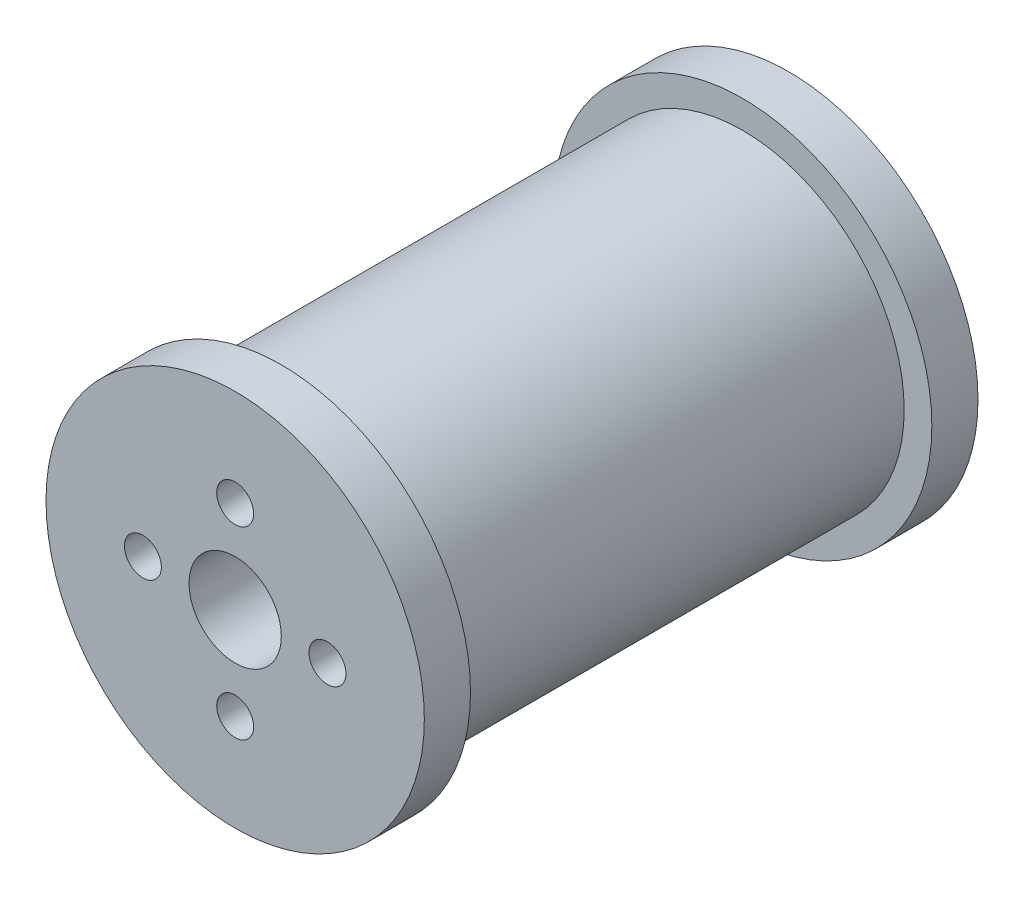
SolidWorks part; units mm, degrees
material "PET"
ref_plane "Front Plane" through (0, 0, 0) normal (0, 0, 1) x (1, 0, 0)
ref_plane "Top Plane" through (0, 0, 0) normal (0, 1, 0) x (1, 0, 0)
ref_plane "Right Plane" through (0, 0, 0) normal (1, 0, 0) x (0, 0, -1)
sketch "Sketch1" plane through (0, 0, 0) normal (0, 0, 1) x (1, 0, 0)
  circle A0 centre (0, 0) radius 17.5
  circle A1 centre (0, 0) radius 5
  circle A2 centre (0, 0) radius 10 construction
  circle A3 centre (0, 10) radius 2
  circle A4 centre (10, 0) radius 2
  circle A5 centre (0, -10) radius 2
  circle A6 centre (-10, 0) radius 2
  point P16 (0, 0)
  dimension "D1" = 35
  dimension "D2" = 10
  dimension "D3" = 20
  dimension "D4" = 4
  dimension "D5" = 4
extrude "Boss-Extrude1" add sketch "Sketch1" along normal blind 50
sketch "Sketch2" plane through (0, 0, 50) normal (0, 0, 1) x (1, 0, 0)
  circle A0 centre (0, 0) radius 20.5
  circle A1 centre (0, 0) radius 17.5 construction
  circle A2 centre (0, 0) radius 5
  circle A3 centre (0, 0) radius 5 construction
  circle A4 centre (0, 0) radius 10 construction
  circle A5 centre (0, 10) radius 2
  circle A6 centre (0, 0) radius 20.5
  circle A7 centre (10, 0) radius 2
  circle A8 centre (0, 0) radius 20.5
  circle A9 centre (0, -10) radius 2
  circle A10 centre (0, 0) radius 20.5
  circle A11 centre (-10, 0) radius 2
  point P23 (0, 0)
  dimension "D1" = 3
  dimension "D2" = 20
  dimension "D3" = 4
  dimension "D4" = 4
extrude "Boss-Extrude2" add sketch "Sketch2" along normal blind 5 contours A11 | A5 | A7 | A9 | A0 | A2
sketch "Sketch3" plane through (0, 0, 0) normal (0, 0, -1) x (-1, 0, 0)
  circle A0 centre (0, 0) radius 20.5
  circle A1 centre (0, 0) radius 20.5 construction
  circle A2 centre (0, 0) radius 5
  circle A3 centre (0, 0) radius 5 construction
  circle A4 centre (0, 0) radius 10 construction
  circle A5 centre (0, 10) radius 2
  circle A7 centre (10, 0) radius 2
  circle A8 centre (0, -10) radius 2
  circle A9 centre (-10, 0) radius 2
  point P20 (0, 0)
  dimension "D1" = 20
  dimension "D2" = 4
  dimension "D3" = 4
extrude "Boss-Extrude3" add sketch "Sketch3" along normal blind 5
